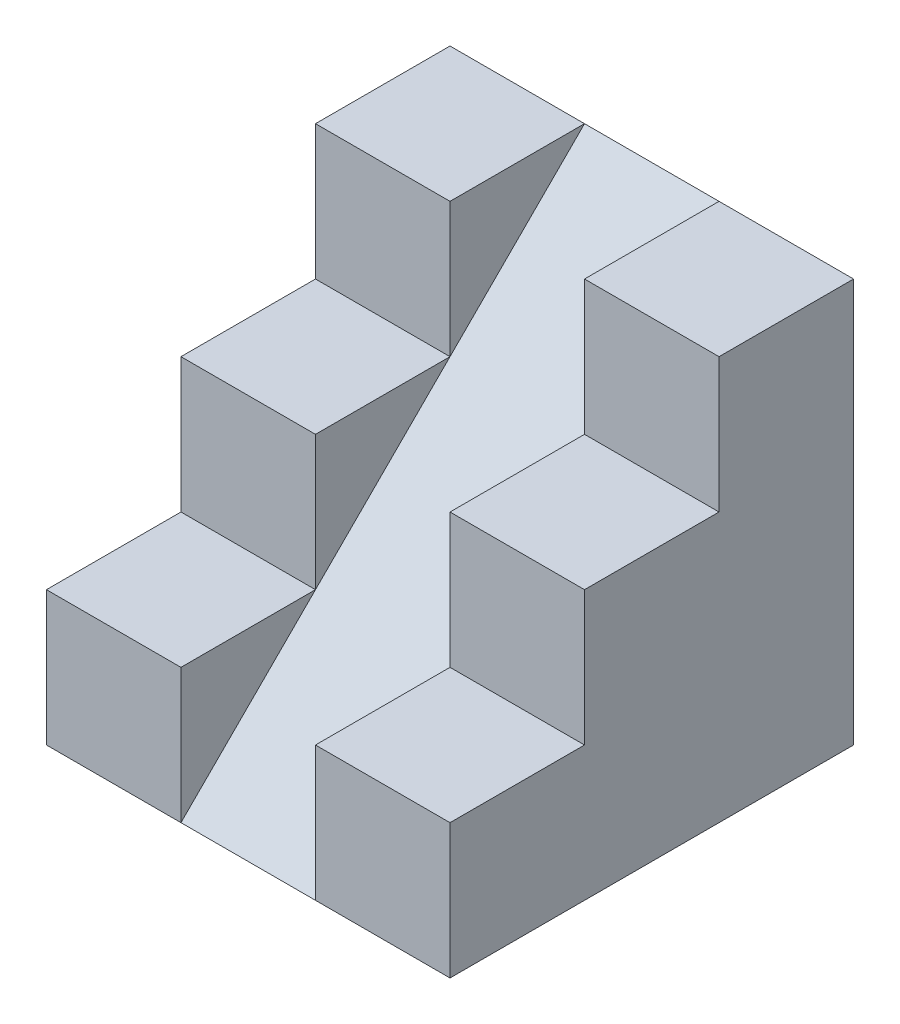
SolidWorks part; units mm, degrees
ref_plane "Alzado" through (0, 0, 0) normal (0, 0, 1) x (1, 0, 0)
ref_plane "Planta" through (0, 0, 0) normal (0, 1, 0) x (1, 0, 0)
ref_plane "Vista lateral" through (0, 0, 0) normal (1, 0, 0) x (0, 0, -1)
sketch "Croquis1" plane through (0, 0, 0) normal (1, 0, 0) x (0, 0, -1)
  line L0 (0, 0) -> (-60, 0)
  line L1 (-60, 0) -> (-60, 20)
  line L2 (-60, 20) -> (-40, 20)
  line L3 (-40, 20) -> (-40, 40)
  line L4 (-40, 40) -> (-20, 40)
  line L5 (-20, 40) -> (-20, 60)
  line L6 (-20, 60) -> (0, 60)
  line L7 (0, 60) -> (0, 0)
  point P7 (-38.3103, 38.3103)
  dimension "D1" = 60
  dimension "D2" = 60
  dimension "D3" = 20
extrude "Saliente-Extruir1" add sketch "Croquis1" along normal mid plane 60
sketch "Croquis2" plane through (0, 0, 0) normal (1, 0, 0) x (0, 0, -1)
  line L0 (0, 60) -> (-20, 60) construction
  line L1 (-20, 60) -> (-20, 40) construction
  line L2 (-20, 40) -> (-40, 40) construction
  line L3 (-40, 40) -> (-40, 20) construction
  line L4 (-40, 20) -> (-60, 20) construction
  line L5 (-60, 20) -> (-60, 0) construction
  line L6 (0, 60) -> (-20, 60)
  line L7 (-20, 60) -> (-20, 40)
  line L8 (-20, 40) -> (-40, 40)
  line L9 (-40, 40) -> (-40, 20)
  line L10 (-40, 20) -> (-60, 20)
  line L11 (-60, 20) -> (-60, 0)
  line L12 (-60, 0) -> (0, 60)
extrude "Cortar-Extruir1" cut sketch "Croquis2" against normal mid plane 20 contours L9 L12 L8 | L11 L12 L10 | L7 L12 L6
